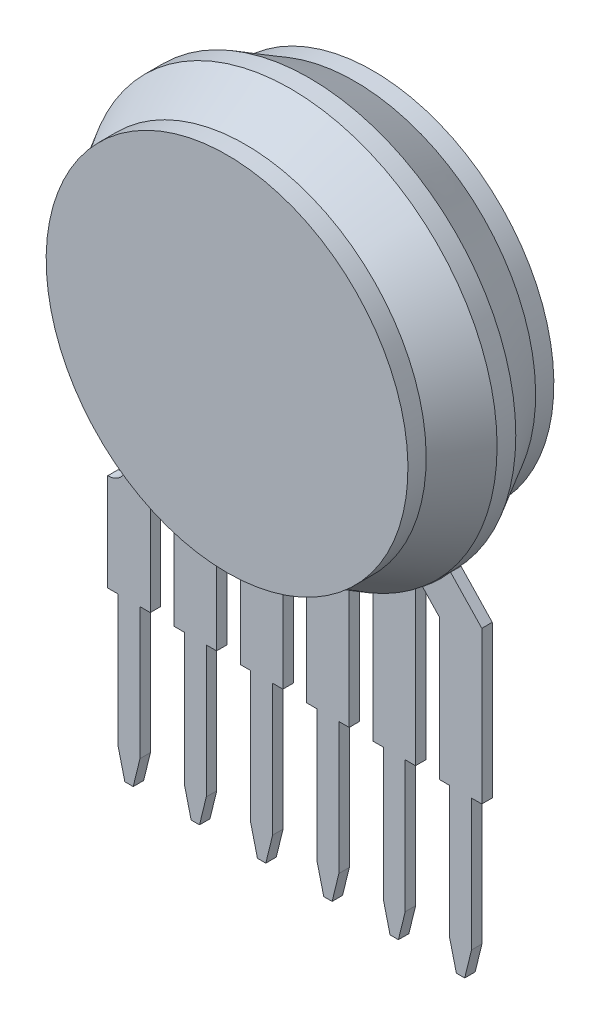
SolidWorks part; units mm, degrees
ref_plane "Front Plane" through (0, 0, 0) normal (0, 0, 1) x (1, 0, 0)
ref_plane "Top Plane" through (0, 0, 0) normal (0, 1, 0) x (1, 0, 0)
ref_plane "Right Plane" through (0, 0, 0) normal (1, 0, 0) x (0, 0, -1)
sketch "Sketch1" plane through (0, 0, 0) normal (0, 0, 1) x (1, 0, 0)
  line L0 (-7.165, -6.4913) -> (-7.165, -7.1728)
  line L1 (-4.625, -8.5934) -> (-4.625, -12.32)
  line L2 (-2.995, -12.32) -> (-2.995, -8.5831)
  line L3 (-7.165, -8.5934) -> (-7.165, -12.32)
  line L4 (-7.165, -12.32) -> (-6.77, -12.32)
  line L5 (-6.77, -12.32) -> (-6.77, -17.3607)
  line L6 (-6.77, -17.3607) -> (-6.5103, -18.42)
  line L7 (-6.5103, -18.42) -> (-6.1897, -18.42)
  line L8 (-6.1897, -18.42) -> (-5.93, -17.3607)
  line L9 (-5.93, -17.3607) -> (-5.93, -12.32)
  line L10 (-5.93, -12.32) -> (-5.535, -12.32)
  line L11 (-5.535, -12.32) -> (-5.535, -8.5831)
  line L12 (-3.39, -12.32) -> (-2.995, -12.32)
  line L13 (-3.39, -17.3607) -> (-3.39, -12.32)
  line L14 (-4.23, -12.32) -> (-4.23, -17.3607)
  line L15 (-4.625, -12.32) -> (-4.23, -12.32)
  line L16 (-3.6497, -18.42) -> (-3.39, -17.3607)
  line L17 (-4.23, -17.3607) -> (-3.9703, -18.42)
  line L18 (-3.9703, -18.42) -> (-3.6497, -18.42)
  line L19 (-2.085, -8.5934) -> (-2.085, -12.32)
  line L20 (-0.455, -12.32) -> (-0.455, -8.5831)
  line L21 (-0.85, -12.32) -> (-0.455, -12.32)
  line L22 (-0.85, -17.3607) -> (-0.85, -12.32)
  line L23 (-1.69, -12.32) -> (-1.69, -17.3607)
  line L24 (-2.085, -12.32) -> (-1.69, -12.32)
  line L25 (-1.1097, -18.42) -> (-0.85, -17.3607)
  line L26 (-1.69, -17.3607) -> (-1.4303, -18.42)
  line L27 (-1.4303, -18.42) -> (-1.1097, -18.42)
  line L28 (0.455, -8.5934) -> (0.455, -12.32)
  line L29 (2.085, -12.32) -> (2.085, -8.5831)
  line L30 (1.69, -12.32) -> (2.085, -12.32)
  line L31 (1.69, -17.3607) -> (1.69, -12.32)
  line L32 (0.85, -12.32) -> (0.85, -17.3607)
  line L33 (0.455, -12.32) -> (0.85, -12.32)
  line L34 (1.4303, -18.42) -> (1.69, -17.3607)
  line L35 (0.85, -17.3607) -> (1.1097, -18.42)
  line L36 (1.1097, -18.42) -> (1.4303, -18.42)
  line L37 (2.995, -8.5934) -> (2.995, -12.32)
  line L38 (4.625, -12.32) -> (4.625, -8.5831)
  line L39 (4.23, -12.32) -> (4.625, -12.32)
  line L40 (4.23, -17.3607) -> (4.23, -12.32)
  line L41 (3.39, -12.32) -> (3.39, -17.3607)
  line L42 (2.995, -12.32) -> (3.39, -12.32)
  line L43 (3.9703, -18.42) -> (4.23, -17.3607)
  line L44 (3.39, -17.3607) -> (3.6497, -18.42)
  line L45 (3.6497, -18.42) -> (3.9703, -18.42)
  line L46 (5.535, -8.5934) -> (5.535, -12.32)
  line L47 (7.165, -12.32) -> (7.165, -8.5831)
  line L48 (6.77, -12.32) -> (7.165, -12.32)
  line L49 (6.77, -17.3607) -> (6.77, -12.32)
  line L50 (5.93, -12.32) -> (5.93, -17.3607)
  line L51 (5.535, -12.32) -> (5.93, -12.32)
  line L52 (6.5103, -18.42) -> (6.77, -17.3607)
  line L53 (5.93, -17.3607) -> (6.1897, -18.42)
  line L54 (6.1897, -18.42) -> (6.5103, -18.42)
  line L55 (-7.165, -8.5934) -> (-4.625, -8.5934) construction
  line L56 (-6.35, -18.42) -> (-6.35, -17.3607) construction
  line L57 (-6.35, -17.3607) -> (-6.77, -17.3607) construction
  line L58 (-5.93, -17.3607) -> (-6.35, -17.3607) construction
  line L59 (0.455, -12.32) -> (0, -12.32) construction
  line L60 (0, -12.32) -> (-0.455, -12.32) construction
  line L62 (0, 0) -> (-11.555, 0) construction
  line L64 (0, 0) -> (0, 0.5736) construction
  line L67 (-7.165, -6.4913) -> (-5.0517, -4.2591)
  line L68 (-5.535, -8.5831) -> (-5.535, -6.9232)
  line L69 (-5.535, -6.9232) -> (-3.8372, -5.1299)
  line L70 (-7.165, -6.4913) -> (-5.535, -6.9232) construction
  line L71 (-6.35, -6.7073) -> (0, 0) construction
  line L72 (0, 0) -> (0, -8.5831) construction
  line L73 (5.535, -6.9232) -> (3.8372, -5.1299)
  line L74 (5.535, -8.5831) -> (5.535, -6.9232)
  line L75 (7.165, -6.4913) -> (5.0517, -4.2591)
  arc A0 (-7.165, -7.1728) -> (-7.165, -8.5934) centre (-7.165, -7.8831) cw
  circle A1 centre (0, 0) radius 0.8115
  circle A2 centre (0, 0) radius 5.401
  circle A7 centre (0, 0) radius 6.8776
  circle A8 centre (0, 0) radius 7.9339
  dimension "D1" = 2.54
  dimension "D2" = 1.63
  dimension "D3" = 0.84
  dimension "D4" = 6.1
  dimension "D5" = 18.42
sketch "Sketch2" plane through (0, 0, 0) normal (1, 0, 0) x (0, 0, -1)
  line L0 (0, -17.9671) -> (-0.2, -17.9671)
  line L3 (-0.2, -17.9671) -> (-0.2, -8.0916)
  line L4 (-0.2, -8.0916) -> (-2.2009, -6.93)
  line L9 (-2.2009, -6.93) -> (-2.795, -6.93)
  line L10 (-2.795, -6.93) -> (-2.795, 6.93)
  line L11 (-2.795, 6.93) -> (-2.0963, 6.93)
  line L14 (-2.0963, 6.93) -> (-0.3582, 7.9084)
  line L15 (-0.3582, 7.9084) -> (0, 7.9084)
  line L18 (0, 7.9084) -> (0, -17.9671)
  line L19 (0, 7.9084) -> (0, 9.9029) construction
  line L20 (2.795, -6.93) -> (2.795, 6.93)
  line L26 (0.2, -17.9671) -> (0.2, -8.0916)
  point P10 (-2.795, 0)
  dimension "D1" = 16
  dimension "D2" = 13.86
  dimension "D3" = 5.59
  dimension "D4" = 0.4
sketch "Sketch7" plane through (0, 0, 0) normal (0, 0, 1) x (1, 0, 0)
  line L1 (-5.93, -12.32) -> (-5.535, -12.32) construction
  line L2 (-5.93, -17.3607) -> (-5.93, -12.32) construction
  line L3 (-6.1897, -18.42) -> (-5.93, -17.3607) construction
  line L4 (-6.5103, -18.42) -> (-6.1897, -18.42) construction
  line L5 (-6.77, -17.3607) -> (-6.5103, -18.42) construction
  line L6 (-6.77, -12.32) -> (-6.77, -17.3607) construction
  line L7 (-7.165, -12.32) -> (-6.77, -12.32) construction
  line L8 (-7.165, -8.5934) -> (-7.165, -12.32) construction
  line L10 (-4.625, -8.5934) -> (-4.625, -12.32) construction
  line L11 (-4.625, -12.32) -> (-4.23, -12.32) construction
  line L12 (-4.23, -12.32) -> (-4.23, -17.3607) construction
  line L13 (-4.23, -17.3607) -> (-3.9703, -18.42) construction
  line L14 (-3.9703, -18.42) -> (-3.6497, -18.42) construction
  line L15 (-3.6497, -18.42) -> (-3.39, -17.3607) construction
  line L16 (-3.39, -17.3607) -> (-3.39, -12.32) construction
  line L17 (-3.39, -12.32) -> (-2.995, -12.32) construction
  line L18 (-2.995, -12.32) -> (-2.995, -8.5831) construction
  line L19 (-0.455, -12.32) -> (-0.455, -8.5831) construction
  line L20 (-0.85, -12.32) -> (-0.455, -12.32) construction
  line L21 (-0.85, -17.3607) -> (-0.85, -12.32) construction
  line L22 (-1.1097, -18.42) -> (-0.85, -17.3607) construction
  line L23 (-1.4303, -18.42) -> (-1.1097, -18.42) construction
  line L24 (-1.69, -17.3607) -> (-1.4303, -18.42) construction
  line L25 (-1.69, -12.32) -> (-1.69, -17.3607) construction
  line L26 (-2.085, -12.32) -> (-1.69, -12.32) construction
  line L27 (-2.085, -8.5934) -> (-2.085, -12.32) construction
  line L28 (4.625, -12.32) -> (4.625, -8.5831) construction
  line L29 (4.23, -12.32) -> (4.625, -12.32) construction
  line L30 (4.23, -17.3607) -> (4.23, -12.32) construction
  line L31 (3.9703, -18.42) -> (4.23, -17.3607) construction
  line L32 (3.6497, -18.42) -> (3.9703, -18.42) construction
  line L33 (3.39, -17.3607) -> (3.6497, -18.42) construction
  line L34 (3.39, -12.32) -> (3.39, -17.3607) construction
  line L35 (2.995, -12.32) -> (3.39, -12.32) construction
  line L36 (2.995, -8.5934) -> (2.995, -12.32) construction
  line L37 (0.455, -8.5934) -> (0.455, -12.32) construction
  line L38 (0.455, -12.32) -> (0.85, -12.32) construction
  line L39 (0.85, -12.32) -> (0.85, -17.3607) construction
  line L40 (0.85, -17.3607) -> (1.1097, -18.42) construction
  line L41 (1.1097, -18.42) -> (1.4303, -18.42) construction
  line L42 (1.4303, -18.42) -> (1.69, -17.3607) construction
  line L43 (1.69, -17.3607) -> (1.69, -12.32) construction
  line L44 (1.69, -12.32) -> (2.085, -12.32) construction
  line L45 (2.085, -12.32) -> (2.085, -8.5831) construction
  line L47 (5.535, -12.32) -> (5.93, -12.32) construction
  line L48 (5.93, -12.32) -> (5.93, -17.3607) construction
  line L49 (5.93, -17.3607) -> (6.1897, -18.42) construction
  line L50 (6.1897, -18.42) -> (6.5103, -18.42) construction
  line L51 (6.5103, -18.42) -> (6.77, -17.3607) construction
  line L52 (6.77, -17.3607) -> (6.77, -12.32) construction
  line L53 (6.77, -12.32) -> (7.165, -12.32) construction
  line L55 (-7.165, -6.4913) -> (-7.165, -7.1728) construction
  line L56 (-5.93, -12.32) -> (-5.535, -12.32)
  line L57 (-5.93, -17.3607) -> (-5.93, -12.32)
  line L58 (-6.1897, -18.42) -> (-5.93, -17.3607)
  line L59 (-6.5103, -18.42) -> (-6.1897, -18.42)
  line L60 (-6.77, -17.3607) -> (-6.5103, -18.42)
  line L61 (-6.77, -12.32) -> (-6.77, -17.3607)
  line L62 (-7.165, -12.32) -> (-6.77, -12.32)
  line L63 (-7.165, -8.5934) -> (-7.165, -12.32)
  line L64 (-7.165, -6.4913) -> (-5.0517, -4.2591) construction
  line L65 (-4.625, -6.4464) -> (-4.625, -12.32)
  line L66 (-4.625, -12.32) -> (-4.23, -12.32)
  line L67 (-4.23, -12.32) -> (-4.23, -17.3607)
  line L68 (-4.23, -17.3607) -> (-3.9703, -18.42)
  line L69 (-3.9703, -18.42) -> (-3.6497, -18.42)
  line L70 (-3.6497, -18.42) -> (-3.39, -17.3607)
  line L71 (-3.39, -17.3607) -> (-3.39, -12.32)
  line L72 (-3.39, -12.32) -> (-2.995, -12.32)
  line L73 (-2.995, -12.32) -> (-2.995, -7.3469)
  line L74 (-0.455, -12.32) -> (-0.455, -7.9208)
  line L75 (-0.85, -12.32) -> (-0.455, -12.32)
  line L76 (-0.85, -17.3607) -> (-0.85, -12.32)
  line L77 (-1.1097, -18.42) -> (-0.85, -17.3607)
  line L78 (-1.4303, -18.42) -> (-1.1097, -18.42)
  line L79 (-1.69, -17.3607) -> (-1.4303, -18.42)
  line L80 (-1.69, -12.32) -> (-1.69, -17.3607)
  line L81 (-2.085, -12.32) -> (-1.69, -12.32)
  line L82 (-2.085, -7.655) -> (-2.085, -12.32)
  line L83 (4.625, -12.32) -> (4.625, -6.4464)
  line L84 (4.23, -12.32) -> (4.625, -12.32)
  line L85 (4.23, -17.3607) -> (4.23, -12.32)
  line L86 (3.9703, -18.42) -> (4.23, -17.3607)
  line L87 (3.6497, -18.42) -> (3.9703, -18.42)
  line L88 (3.39, -17.3607) -> (3.6497, -18.42)
  line L89 (3.39, -12.32) -> (3.39, -17.3607)
  line L90 (2.995, -12.32) -> (3.39, -12.32)
  line L91 (2.995, -7.3469) -> (2.995, -12.32)
  line L92 (0.455, -7.9208) -> (0.455, -12.32)
  line L93 (0.455, -12.32) -> (0.85, -12.32)
  line L94 (0.85, -12.32) -> (0.85, -17.3607)
  line L95 (0.85, -17.3607) -> (1.1097, -18.42)
  line L96 (1.1097, -18.42) -> (1.4303, -18.42)
  line L97 (1.4303, -18.42) -> (1.69, -17.3607)
  line L98 (1.69, -17.3607) -> (1.69, -12.32)
  line L99 (1.69, -12.32) -> (2.085, -12.32)
  line L100 (2.085, -12.32) -> (2.085, -7.655)
  line L101 (-5.535, -8.5831) -> (-5.535, -6.9232) construction
  line L102 (5.535, -12.32) -> (5.93, -12.32)
  line L103 (5.93, -12.32) -> (5.93, -17.3607)
  line L104 (5.93, -17.3607) -> (6.1897, -18.42)
  line L105 (6.1897, -18.42) -> (6.5103, -18.42)
  line L106 (6.5103, -18.42) -> (6.77, -17.3607)
  line L107 (6.77, -17.3607) -> (6.77, -12.32)
  line L108 (6.77, -12.32) -> (7.165, -12.32)
  line L109 (-5.535, -6.9232) -> (-3.8372, -5.1299) construction
  line L110 (7.165, -6.4913) -> (5.0517, -4.2591) construction
  line L111 (5.535, -6.9232) -> (3.8372, -5.1299) construction
  line L112 (5.535, -8.5831) -> (5.535, -6.9232) construction
  line L113 (7.165, -12.32) -> (7.165, -8.5831) construction
  line L114 (-7.165, -6.4913) -> (-7.165, -7.1728)
  line L115 (-7.165, -6.4913) -> (-5.9684, -5.2274)
  line L116 (-5.535, -12.32) -> (-5.535, -6.9232)
  line L117 (-5.535, -6.9232) -> (-4.8932, -6.2453)
  line L118 (7.165, -6.4913) -> (5.9684, -5.2274)
  line L119 (5.535, -6.9232) -> (4.8932, -6.2453)
  line L120 (5.535, -12.32) -> (5.535, -6.9232)
  line L121 (7.165, -12.32) -> (7.165, -6.4913)
  arc A0 (-7.165, -8.5934) -> (-7.165, -7.1728) centre (-7.165, -7.8831) ccw construction
  arc A1 (-7.165, -8.5934) -> (-7.165, -7.1728) centre (-7.165, -7.8831) ccw
  circle A2 centre (0, 0) radius 7.9339 construction
  arc A3 (-5.9684, -5.2274) -> (-4.8932, -6.2453) centre (0, 0) ccw
  arc A4 (-2.085, -7.655) -> (-0.455, -7.9208) centre (0, 0) ccw
  arc A5 (0.455, -7.9208) -> (2.085, -7.655) centre (0, 0) ccw
  arc A6 (2.995, -7.3469) -> (4.625, -6.4464) centre (0, 0) ccw
  arc A7 (4.8932, -6.2453) -> (5.9684, -5.2274) centre (0, 0) ccw
  arc A8 (-4.625, -6.4464) -> (-2.995, -7.3469) centre (0, 0) ccw
extrude "Extrude6" add sketch "Sketch7" along normal up to vertex (0.2 mm away) and the other way up to vertex (0.2 mm away) up to point (0, -17.9671, 0.2) other way up to point (0, -17.9671, -0.2)
sketch "Sketch8" plane through (0, 0, 0) normal (1, 0, 0) x (0, 0, -1)
  line L1 (2.795, -6.93) -> (2.795, 6.93) construction
  line L2 (0, 7.9339) -> (0, -7.9339) construction
  line L3 (2.795, 0) -> (2.795, 6.93)
  line L4 (0, 7.9339) -> (0, -7.9339) construction
  line L5 (0.3582, 7.9084) -> (2.0963, 6.93)
  line L6 (2.795, 0) -> (8.385, 0) construction
  line L7 (2.0963, 6.93) -> (2.795, 6.93)
  line L8 (-2.795, 0) -> (2.795, 0)
  line L13 (-0.2, -17.9671) -> (0, -17.9671)
  line L14 (-0.2, -8.0916) -> (-0.2, -17.9671)
  line L15 (-2.2009, -6.93) -> (-0.2, -8.0916)
  line L16 (-2.795, -6.93) -> (-2.2009, -6.93)
  line L17 (-2.795, 6.93) -> (-2.795, -6.93)
  line L18 (-2.0963, 6.93) -> (-2.795, 6.93)
  line L19 (-0.3582, 7.9084) -> (-2.0963, 6.93)
  line L20 (0, 7.9084) -> (-0.3582, 7.9084)
  line L21 (0, -17.9671) -> (0, 7.9084)
  line L26 (-2.795, 6.93) -> (-2.795, 0)
  line L27 (-2.0963, 6.93) -> (-2.795, 6.93)
  line L28 (-0.3582, 7.9084) -> (-2.0963, 6.93)
  line L29 (0.3582, 7.9084) -> (-0.3582, 7.9084)
  dimension "D1" = 0
revolve "Revolve1" add sketch "Sketch8" angle 360 about L6
